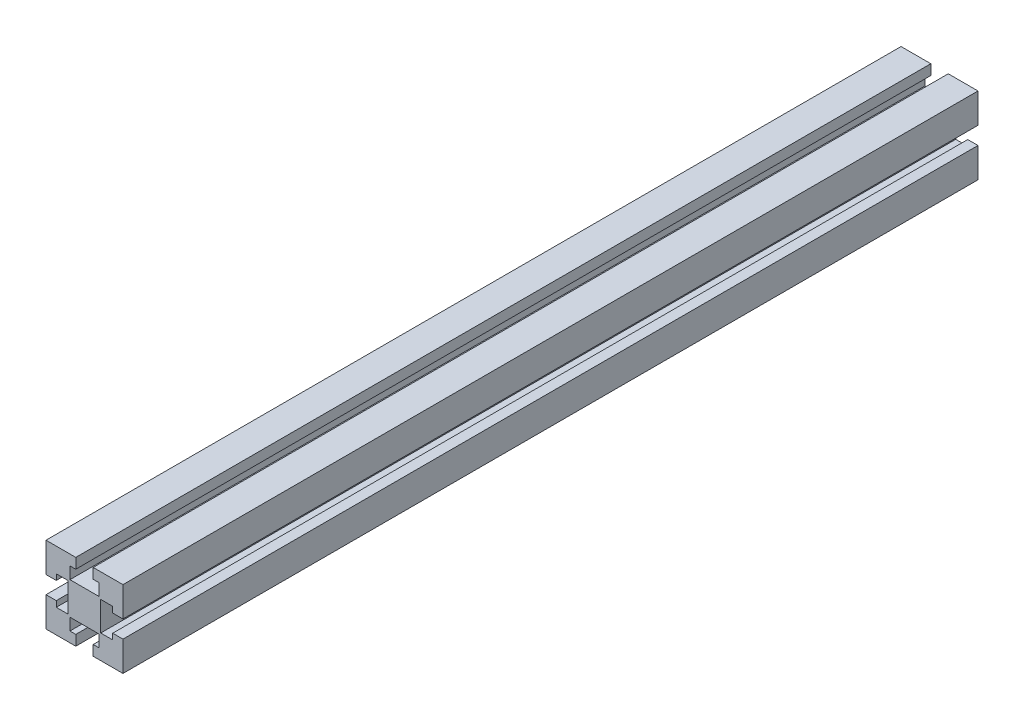
SolidWorks part; units mm, degrees
ref_plane "Ebene vorne" through (0, 0, 0) normal (0, 0, 1) x (1, 0, 0)
ref_plane "Ebene oben" through (0, 0, 0) normal (0, 1, 0) x (1, 0, 0)
ref_plane "Ebene rechts" through (0, 0, 0) normal (1, 0, 0) x (0, 0, -1)
sketch "Skizze1" plane through (0, 0, 0) normal (0, 0, 1) x (1, 0, 0)
  line L39 (-18.8192, 33.7768) -> (-1.4192, 33.7768)
  line L43 (-46.4192, 33.7768) -> (-29.0192, 33.7768)
  line L44 (-46.4192, 33.7768) -> (-46.4192, 16.3768)
  line L45 (-46.4192, -11.2232) -> (-29.0192, -11.2232)
  line L46 (-1.4192, 33.7768) -> (-1.4192, 16.3768)
  line L47 (-32.4242, 27.7768) -> (-29.0192, 27.7768)
  line L48 (-32.4242, 27.7768) -> (-32.4242, 20.7768)
  line L49 (-32.4242, 20.7768) -> (-15.4143, 20.7768)
  line L50 (-15.4143, 27.7768) -> (-15.4143, 20.7768)
  line L51 (-14.4192, 19.7817) -> (-7.4192, 19.7817)
  line L52 (-14.4192, 19.7817) -> (-14.4192, 2.7718)
  line L53 (-14.4192, 2.7718) -> (-7.4192, 2.7718)
  line L54 (-7.4192, 19.7817) -> (-7.4192, 16.3768)
  line L55 (-32.4242, 1.7768) -> (-15.4143, 1.7768)
  line L56 (-32.4242, 1.7768) -> (-32.4242, -5.2232)
  line L57 (-32.4242, -5.2232) -> (-29.0192, -5.2232)
  line L58 (-15.4143, 1.7768) -> (-15.4143, -5.2232)
  line L59 (-40.4192, 19.7817) -> (-33.4192, 19.7817)
  line L60 (-40.4192, 19.7817) -> (-40.4192, 16.3768)
  line L61 (-40.4192, 2.7718) -> (-33.4192, 2.7718)
  line L62 (-33.4192, 19.7817) -> (-33.4192, 2.7718)
  line L64 (-29.0192, 27.7768) -> (-29.0192, 33.7768)
  line L66 (-18.8192, 27.7768) -> (-18.8192, 33.7768)
  line L67 (-7.4192, 16.3768) -> (-1.4192, 16.3768)
  line L69 (-7.4192, 6.1768) -> (-1.4192, 6.1768)
  line L72 (-29.0192, -5.2232) -> (-29.0192, -11.2232)
  line L74 (-18.8192, -5.2232) -> (-18.8192, -11.2232)
  line L75 (-40.4192, 16.3768) -> (-46.4192, 16.3768)
  line L77 (-40.4192, 6.1768) -> (-46.4192, 6.1768)
  line L79 (-18.8192, 27.7768) -> (-15.4143, 27.7768)
  line L80 (-7.4192, 6.1768) -> (-7.4192, 2.7718)
  line L81 (-1.4192, 6.1768) -> (-1.4192, -11.2232)
  line L82 (-18.8192, -11.2232) -> (-1.4192, -11.2232)
  line L83 (-18.8192, -5.2232) -> (-15.4143, -5.2232)
  line L84 (-46.4192, 6.1768) -> (-46.4192, -11.2232)
  line L85 (-40.4192, 6.1768) -> (-40.4192, 2.7718)
  dimension "D6" = 13
  dimension "D4" = 13
  dimension "D1" = 10.2
  dimension "D2" = 45
  dimension "D3" = 45
  dimension "D5" = 13
  dimension "D7" = 13
  dimension "D8" = 6
  dimension "D9" = 13.995
extrude "Aufsatz-Linear austragen1" add sketch "Skizze1" along normal blind 500 contours L43 L64 L47 L48 L49 L50 L79 L66 L39 L46 L67 L54 L51 L52 L53 L80 L69 L81 L82 L74 L83 L58 L55 L56 L57 L72 L45 L84 L77 L85 L61 L62 L59 L60 L75 L44
